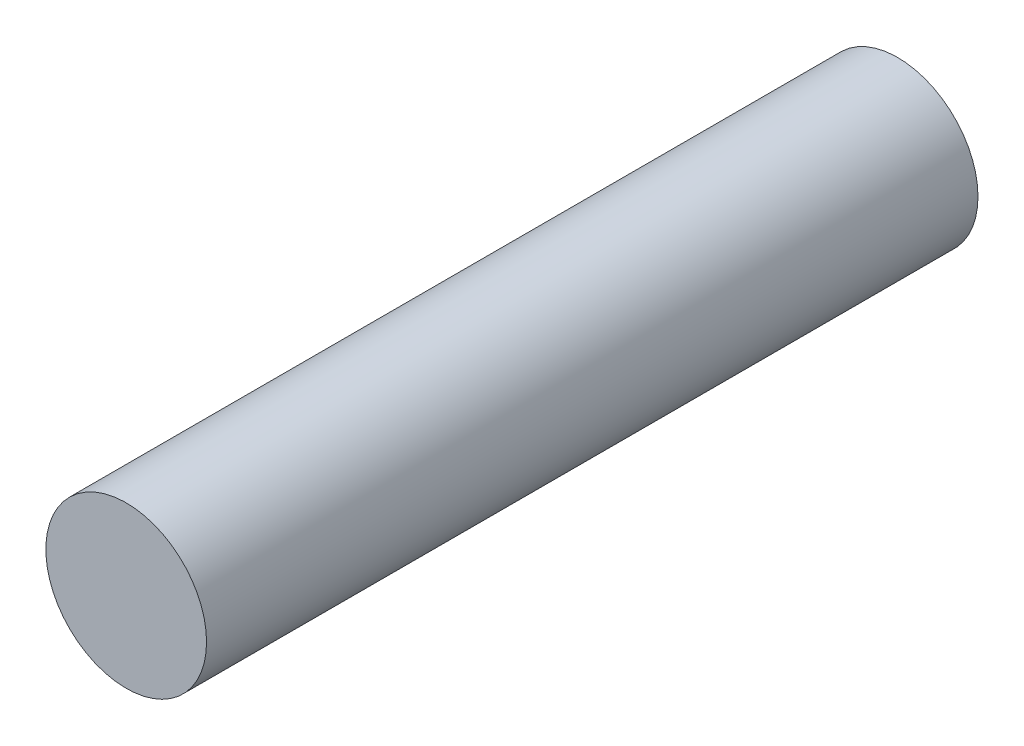
SolidWorks part; units mm, degrees
material "AISI 304"
ref_plane "Front Plane" through (0, 0, 0) normal (0, 0, 1) x (1, 0, 0)
ref_plane "Top Plane" through (0, 0, 0) normal (0, 1, 0) x (1, 0, 0)
ref_plane "Right Plane" through (0, 0, 0) normal (1, 0, 0) x (0, 0, -1)
sketch "Sketch1" plane through (0, 0, 0) normal (0, 0, 1) x (1, 0, 0)
  circle A0 centre (0, 0) radius 7.5
  dimension "D1" = 15
extrude "Boss-Extrude1" add sketch "Sketch1" along normal mid plane 72
